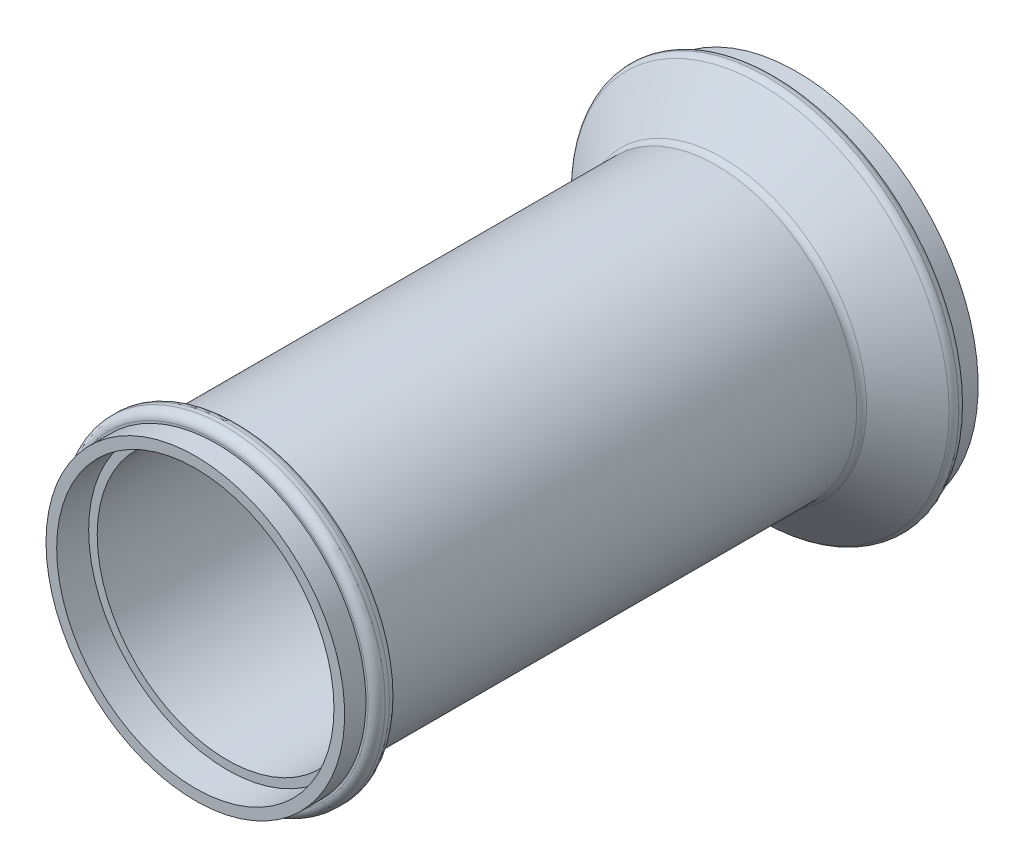
SolidWorks part; units mm, degrees
ref_plane "Front Plane" through (0, 0, 0) normal (0, 0, 1) x (1, 0, 0)
ref_plane "Top Plane" through (0, 0, 0) normal (0, 1, 0) x (1, 0, 0)
ref_plane "Right Plane" through (0, 0, 0) normal (1, 0, 0) x (0, 0, -1)
sketch "Sketch1" plane through (0, 0, 0) normal (0, 1, 0) x (1, 0, 0)
  line L0 (0, 0) -> (0, -141)
  line L1 (0, 0) -> (42.5, 0)
  line L2 (42.5, 0) -> (42.5, -5)
  line L3 (42.5, -5) -> (45, -5)
  line L4 (45, -5) -> (45, -8)
  line L5 (45, -8) -> (33, -18)
  line L6 (33, -18) -> (33, -131)
  line L7 (33, -131) -> (37.5, -131)
  line L8 (37.5, -131) -> (37.5, -136)
  line L9 (37.5, -136) -> (35, -136)
  line L10 (35, -136) -> (35, -141)
  line L11 (35, -141) -> (0, -141)
  dimension "D1" = 42.5
  dimension "D2" = 5
  dimension "D3" = 3
  dimension "D4" = 45
  dimension "D5" = 33
  dimension "D6" = 18
  dimension "D7" = 131
  dimension "D8" = 37.5
  dimension "D9" = 5
  dimension "D10" = 35
  dimension "D11" = 141
revolve "Revolve1" add sketch "Sketch1" angle 360 about L0
fillet "Fillet1" radius 2 6 edges at (-37.5, 0, 136) (-37.5, 0, 131) (-33, 0, 131) (-33, 0, 18) (-45, 0, 8) (-45, 0, 5)
sketch "Sketch2" plane through (0, 0, 0) normal (0, 1, 0) x (1, 0, 0)
  line L9 (40, 0) -> (40, -8.9124)
  line L10 (41.6949, -7.5) -> (40, -8.9124) construction
  line L11 (40, 0) -> (0, 0)
  line L12 (0, 0) -> (0, -141)
  line L13 (-35, -141) -> (35, -141) construction
  line L14 (0, -141) -> (32.5, -141)
  line L18 (32.5, -133.5) -> (32.5, -141)
  line L19 (30.5, -133.5) -> (32.5, -133.5)
  line L20 (30.5, -16.8291) -> (30.5, -133.5)
  line L21 (41.6949, -7.5) -> (30.5, -16.8291)
  line L22 (40, -7.5) -> (41.6949, -7.5)
  line L23 (40, 0) -> (40, -7.5)
  line L24 (32.5, -133.5) -> (32.5, -141)
  line L25 (30.5, -133.5) -> (32.5, -133.5)
  line L26 (30.5, -16.8291) -> (30.5, -133.5)
  line L27 (40, -8.9124) -> (30.5, -16.8291)
  line L28 (40, -7.5) -> (41.6949, -7.5) construction
  line L29 (40, 0) -> (40, -7.5) construction
  dimension "D1" = 2.5
revolve "Cut-Revolve1" cut sketch "Sketch2" angle 360 about L12
